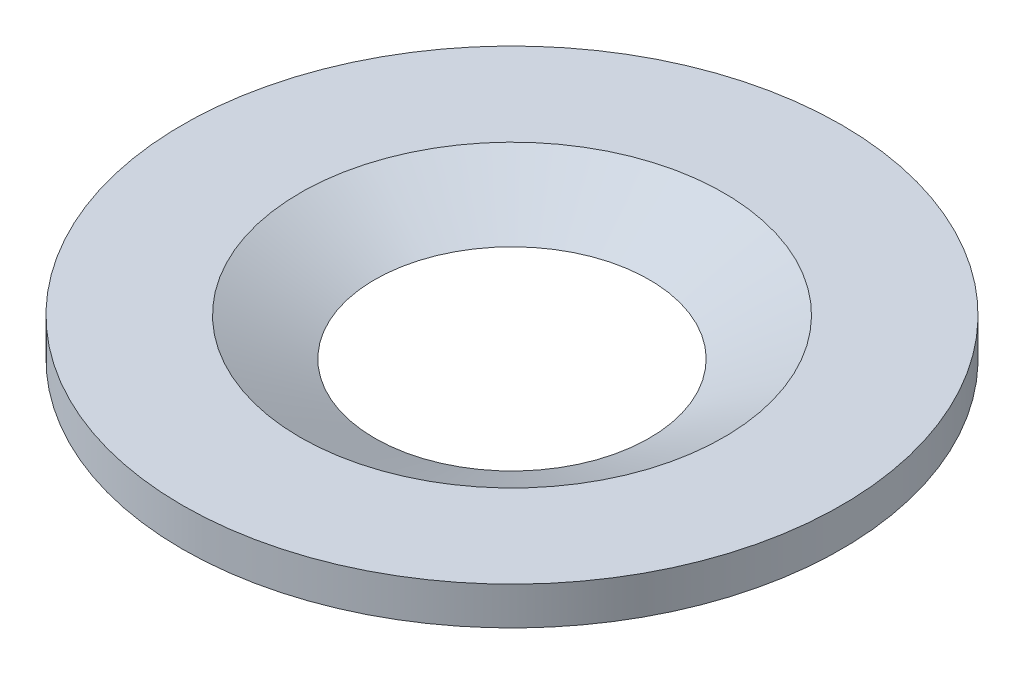
SolidWorks part; units mm, degrees
ref_plane "Front Plane" through (0, 0, 0) normal (0, 0, 1) x (1, 0, 0)
ref_plane "Top Plane" through (0, 0, 0) normal (0, 1, 0) x (1, 0, 0)
ref_plane "Right Plane" through (0, 0, 0) normal (1, 0, 0) x (0, 0, -1)
sketch "Sketch1" plane through (0, 0, 0) normal (0, 1, 0) x (1, 0, 0)
  circle A0 centre (0, 0) radius 83.82
  circle A1 centre (0, 0) radius 34.925
  dimension "D1" = 167.64
  dimension "D2" = 69.85
extrude "Boss-Extrude1" add sketch "Sketch1" along normal blind 9.652
sketch "Sketch4" plane through (0, 0, 0) normal (0, 0, 1) x (1, 0, 0)
  line L0 (0, 23.2786) -> (0, -14.9525) construction
sketch "Sketch3" plane through (0, 0, 0) normal (0, 0, 1) x (1, 0, 0)
  line L0 (-34.925, 0) -> (-53.8681, 9.652)
  line L1 (83.82, 9.652) -> (-83.82, 9.652) construction
  line L2 (-53.8681, 9.652) -> (-34.925, 9.652)
  line L3 (-34.925, 9.652) -> (-34.925, 0)
  dimension "D1" = 27
revolve "Cut-Revolve1" cut sketch "Sketch3" angle 360 about L0
